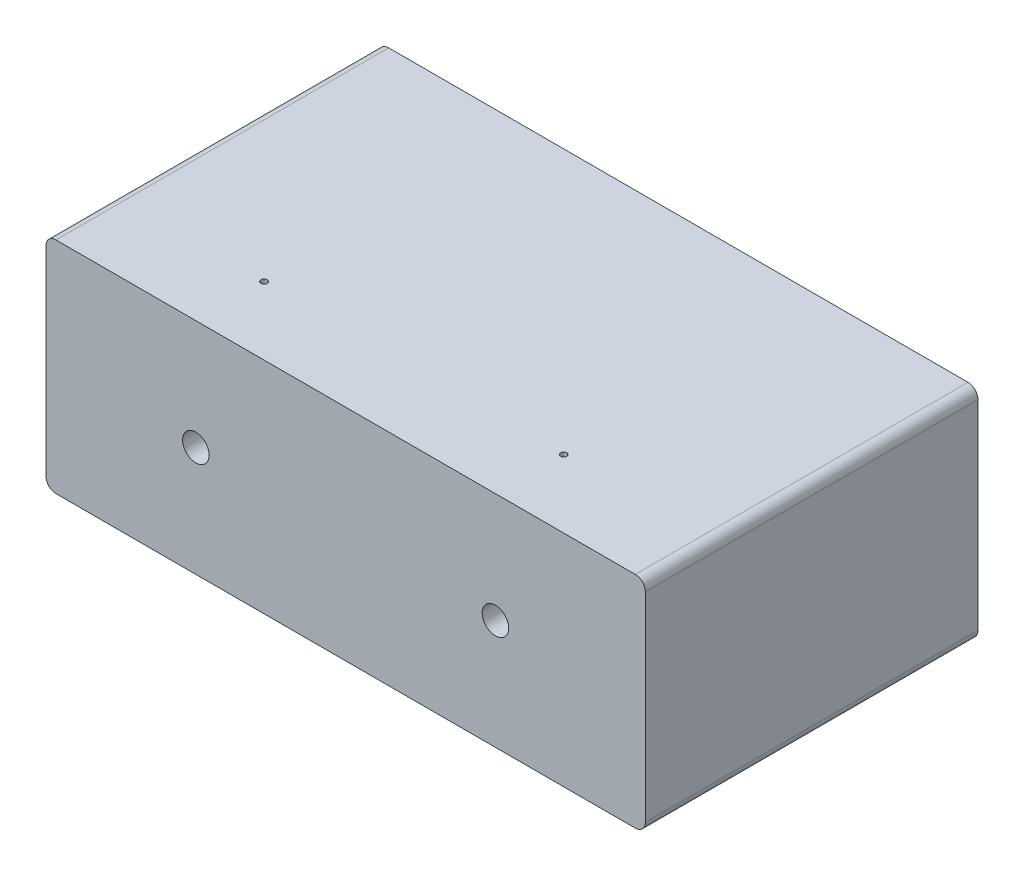
SolidWorks part; units mm, degrees
material "304, 316 OR 302 SSTL"
ref_plane "Front" through (0, 0, 0) normal (0, 0, 1) x (1, 0, 0)
ref_plane "Top" through (0, 0, 0) normal (0, 1, 0) x (1, 0, 0)
ref_plane "Right" through (0, 0, 0) normal (1, 0, 0) x (0, 0, -1)
sketch "Sketch1" plane through (0, 0, 0) normal (0, 1, 0) x (1, 0, 0)
  line L1 (76.2, -42.3037) -> (-76.2, -42.3037)
  line L2 (76.2, -42.3037) -> (76.2, 42.3037)
  line L3 (76.2, 42.3037) -> (-76.2, 42.3037)
  line L4 (-76.2, -42.3037) -> (-76.2, 42.3037)
  line L5 (76.2, -42.3037) -> (-76.2, 42.3037) construction
  line L6 (76.2, 42.3037) -> (-76.2, -42.3037) construction
  point P0 (0, 0)
  dimension "D1" = 152.4
  dimension "D2" = 84.6074
extrude "Extrude1" add sketch "Sketch1" along normal blind 55.88
fillet "Fillet1" radius 2.54 4 edges at (-76.2, 0, 0) (76.2, 0, 0) (76.2, 55.88, 0) (-76.2, 55.88, 0)
hole_wizard "Tapped Hole for 1/4-20 Helicoil1" positions "Sketch3" profile "Sketch2" tap size "1/4-20" standard "Helicoil® Inch"
sketch "Sketch3" plane through (0, 0, 42.3037) normal (0, 0, 1) x (1, 0, 0)
  line L0 (-73.66, 55.88) -> (73.66, 55.88) construction
  line L1 (-73.66, 0) -> (73.66, 0) construction
  point P0 (-38.1, 27.94)
  point P1 (38.1, 27.94)
  point P8 (0, 0)
  dimension "D1" = 27.94
  dimension "D2" = 38.1
  dimension "D3" = 27.94
  dimension "D4" = 38.1
sketch "Sketch2" plane through (-38.1, 27.94, 42.3037) normal (1, 0, 0) x (0, -1, 0)
  line L0 (0, 0) -> (0, 21.7148)
  line L1 (0, 21.7148) -> (3.3782, 19.685)
  line L2 (3.3782, 19.685) -> (3.3782, 0)
  line L5 (3.3782, 0) -> (0, 0)
  line L10 (0, 21.7148) -> (-3.3782, 19.685) construction
  line L11 (0, -6.35) -> (0, 107.95) construction
  dimension "Tap Drill Dia." = 6.7564
  dimension "Tap Drill Depth" = 19.685
  dimension "Drill Angle" = 118
hole_wizard "1/16 (0.0625) Diameter Hole1" positions "Sketch5" profile "Sketch4" hole size "1/16" standard "Ansi Inch"
sketch "Sketch5" plane through (0, 55.88, 0) normal (0, 1, 0) x (-1, 0, 0)
  point P0 (-38.161, 25.0114)
  point P4 (38.039, 25.0114)
  dimension "D1" = 76.2
sketch "Sketch4" plane through (38.161, 55.88, 25.0114) normal (1, 0, 0) x (0, 0, 1)
  line L0 (0, 0) -> (0, 28.4169)
  line L1 (0, 28.4169) -> (0.7937, 27.94)
  line L2 (0.7937, 27.94) -> (0.7937, 0)
  line L5 (0.7937, 0) -> (0, 0)
  line L10 (0, 28.4169) -> (-0.7938, 27.94) construction
  line L11 (0, -6.35) -> (0, 107.95) construction
  dimension "Hole Dia." = 1.5875
  dimension "Hole Depth" = 27.94
  dimension "Drill Angle" = 118
